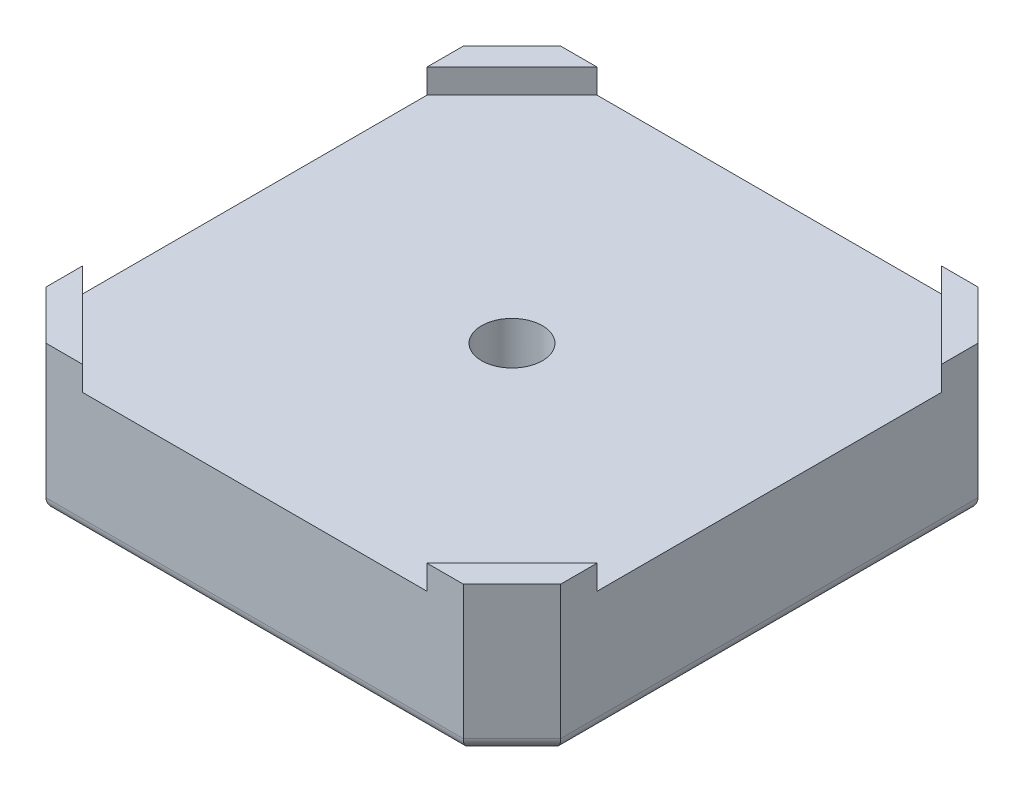
SolidWorks part; units mm, degrees
ref_plane "Front Plane" through (0, 0, 0) normal (0, 0, 1) x (1, 0, 0)
ref_plane "Top Plane" through (0, 0, 0) normal (0, 1, 0) x (1, 0, 0)
ref_plane "Right Plane" through (0, 0, 0) normal (1, 0, 0) x (0, 0, -1)
sketch "Sketch10" plane through (0, 0, 0) normal (0, 1, 0) x (1, 0, 0)
  line L0 (-21.15, 17.15) -> (-17.15, 21.15)
  line L1 (-17.15, -21.15) -> (17.15, -21.15)
  line L2 (-21.15, -17.15) -> (-21.15, 17.15)
  line L3 (-17.15, 21.15) -> (17.15, 21.15)
  line L4 (21.15, -17.15) -> (21.15, 17.15)
  line L5 (-21.15, -21.15) -> (21.15, 21.15) construction
  line L6 (-21.15, 21.15) -> (21.15, -21.15) construction
  line L7 (21.15, 17.15) -> (17.15, 21.15)
  line L8 (17.15, -21.15) -> (21.15, -17.15)
  line L9 (-21.15, -17.15) -> (-17.15, -21.15)
  point P0 (0, 0)
  dimension "D1" = 42.3
  dimension "D2" = 42.3
extrude "Boss-Extrude3" add sketch "Sketch10" along normal blind 12
sketch "Sketch11" plane through (0, 12, 0) normal (0, 1, 0) x (1, 0, 0)
  line L0 (21.15, -17.15) -> (21.15, 17.15) construction
  line L1 (-14.15, -21.15) -> (14.15, -21.15)
  line L2 (-21.15, -14.15) -> (-21.15, 14.15)
  line L3 (-14.15, 21.15) -> (14.15, 21.15)
  line L4 (21.15, -14.15) -> (21.15, 14.15)
  line L5 (-21.15, -21.15) -> (21.15, 21.15) construction
  line L6 (-21.15, 21.15) -> (21.15, -21.15) construction
  line L7 (17.15, 21.15) -> (-17.15, 21.15) construction
  line L8 (-21.15, 14.15) -> (-14.15, 21.15)
  line L9 (-21.15, -14.15) -> (-14.15, -21.15)
  line L10 (14.15, -21.15) -> (21.15, -14.15)
  line L11 (21.15, 14.15) -> (14.15, 21.15)
  point P0 (0, 0)
extrude "Cut-Extrude5" cut sketch "Sketch11" against normal blind 2
sketch "Sketch12" plane through (0, 10, 0) normal (0, 1, 0) x (1, 0, 0)
  circle A0 centre (0, 0) radius 2.5
  dimension "D1" = 5
extrude "Cut-Extrude6" cut sketch "Sketch12" against normal through all
sketch "Sketch13" plane through (0, 0, 0) normal (0, -1, 0) x (1, 0, 0)
  circle A0 centre (0, 0) radius 5.5
  dimension "D1" = 11
extrude "Cut-Extrude7" cut sketch "Sketch13" against normal blind 5
sketch "Sketch14" plane through (0, 0, 0) normal (0, -1, 0) x (1, 0, 0)
  line L1 (-15.5, -15.5) -> (15.5, -15.5) construction
  line L2 (-15.5, -15.5) -> (-15.5, 15.5) construction
  line L3 (-15.5, 15.5) -> (15.5, 15.5) construction
  line L4 (15.5, -15.5) -> (15.5, 15.5) construction
  line L5 (-15.5, -15.5) -> (15.5, 15.5) construction
  line L6 (-15.5, 15.5) -> (15.5, -15.5) construction
  circle A0 centre (-15.5, 15.5) radius 1.5
  circle A1 centre (15.5, 15.5) radius 1.5
  circle A2 centre (15.5, -15.5) radius 1.5
  circle A3 centre (-15.5, -15.5) radius 1.5
  circle A4 centre (0, 0) radius 2.5 construction
  circle A5 centre (0, 0) radius 5.5 construction
  point P0 (0, 0)
  point P16 (0, 0)
  dimension "D2" = 3
  dimension "D4" = 21.9203
  dimension "D5" = 15.5
  dimension "D1" = 31
  dimension "D3" = 4
sketch "Sketch16" plane through (0, 0, 0) normal (0, -1, 0) x (1, 0, 0)
  circle A0 centre (0, 0) radius 5.5 construction
  circle A1 centre (0, 0) radius 5.5
  circle A2 centre (0, 0) radius 11
  dimension "D1" = 22
extrude "Boss-Extrude4" add sketch "Sketch16" along normal blind 2
fillet "Fillet3" radius 1 8 edges at (-19.15, 0, -19.15) (0, 0, -21.15) (19.15, 0, -19.15) (21.15, 0, 0) (19.15, 0, 19.15) (0, 0, 21.15) (-19.15, 0, 19.15) (-21.15, 0, 0)
fillet "Fillet4" radius 0.5 3 edges at (0, -2, -5.5) (0, -2, -11) (0, 0, 11)
hole_wizard "M3 Tapped Hole1" positions "Sketch17" profile "Sketch18" tap size "M3" standard "ISO"
sketch "Sketch17" plane through (0, 0, 0) normal (0, -1, 0) x (-1, 0, 0)
  point P0 (-15.5, -15.5)
  point P3 (15.5, -15.5)
  point P6 (15.5, 15.5)
  point P9 (-15.5, 15.5)
sketch "Sketch18" plane through (15.5, 0, 15.5) normal (1, 0, 0) x (0, 0, -1)
  line L0 (0, 0) -> (0, 8.2511)
  line L1 (0, 8.2511) -> (1.25, 7.5)
  line L2 (1.25, 7.5) -> (1.25, 0)
  line L5 (1.25, 0) -> (0, 0)
  line L10 (0, 8.2511) -> (-1.25, 7.5) construction
  line L11 (0, -6.35) -> (0, 107.95) construction
  dimension "Tap Drill Dia." = 2.5
  dimension "Tap Drill Depth" = 7.5
  dimension "Drill Angle" = 118
cosmetic thread "Hole Thread1" parameters "D1"=6, "D2"=3
cosmetic thread "Hole Thread2" parameters "D1"=6, "D2"=3
cosmetic thread "Hole Thread3" parameters "D1"=6, "D2"=3
cosmetic thread "Hole Thread4" parameters "D1"=6, "D2"=3
chamfer "Chamfer1" distance 0.3 angle 45 4 edges at (15.5, 0, -16.75) (15.5, 0, 14.25) (-15.5, 0, -16.75) (-15.5, 0, 14.25)
